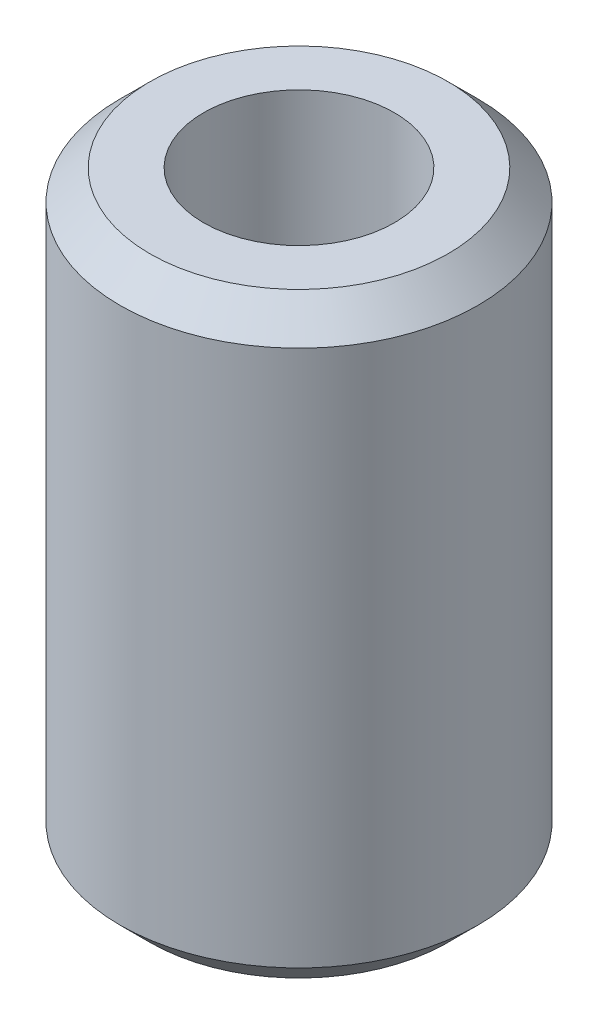
SolidWorks part; units mm, degrees
ref_plane "Front" through (0, 0, 0) normal (0, 0, 1) x (1, 0, 0)
ref_plane "Top" through (0, 0, 0) normal (0, 1, 0) x (1, 0, 0)
ref_plane "Right" through (0, 0, 0) normal (1, 0, 0) x (0, 0, -1)
sketch "Sketch1" plane through (0, 0, 0) normal (0, 1, 0) x (1, 0, 0)
  circle A0 centre (0, 0) radius 3
  dimension "D1" = 6
extrude "Boss-Extrude1" add sketch "Sketch1" along normal blind 10
sketch "Sketch2" plane through (0, 10, 0) normal (0, 1, 0) x (1, 0, 0)
  circle A0 centre (0, 0) radius 1.6
  dimension "D1" = 3.2
extrude "Cut-Extrude1" cut sketch "Sketch2" against normal blind 10
chamfer "Chamfer1" distance 0.5 angle 45 2 edges at (0, 0, 3) (0, 10, 3)
